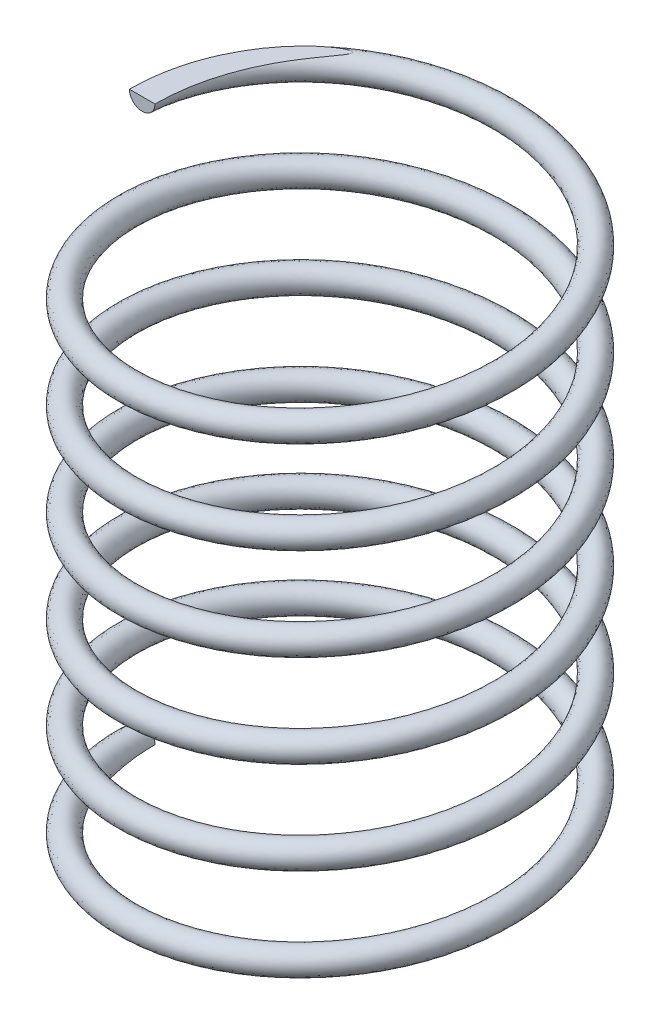
SolidWorks part; units mm, degrees
ref_plane "Front Plane" through (0, 0, 0) normal (0, 0, 1) x (1, 0, 0)
ref_plane "Top Plane" through (0, 0, 0) normal (0, 1, 0) x (1, 0, 0)
ref_plane "Right Plane" through (0, 0, 0) normal (1, 0, 0) x (0, 0, -1)
sketch "Sketch1" plane through (0, 0, 0) normal (0, 1, 0) x (1, 0, 0)
  circle A1 centre (0, 0) radius 4.4
  dimension "D1" = 8.8
curve "Helix/Spiral1" pitch 2.1667 height 13 turns 6
sketch "Sketch5" plane through (0, 0, 0) normal (0, 0, 1) x (1, 0, 0)
  circle A0 centre (-4.4, 0) radius 0.3
  spline S0 degree 3 poles (-4.4, 0) (-4.4, -0.0449) (-4.1709, -0.1356) (-3.1923, -0.2708) (-1.7276, -0.4063) (0, -0.5417) (1.7276, -0.6771) (3.1923, -0.8125) (4.1709, -0.9479) (4.5145, -1.0833) (4.1709, -1.2188) (3.1923, -1.3542) (1.7276, -1.4896) (0, -1.625) (-1.7276, -1.7604) (-3.1923, -1.8958) (-4.1709, -2.0313) (-4.5145, -2.1667) (-4.1709, -2.3021) (-3.1923, -2.4375) (-1.7276, -2.5729) (0, -2.7083) (1.7276, -2.8438) (3.1923, -2.9792) (4.1709, -3.1146) (4.5145, -3.25) (4.1709, -3.3854) (3.1923, -3.5208) (1.7276, -3.6562) (0, -3.7917) (-1.7276, -3.9271) (-3.1923, -4.0625) (-4.1709, -4.1979) (-4.5145, -4.3333) (-4.1709, -4.4687) (-3.1923, -4.6042) (-1.7276, -4.7396) (0, -4.875) (1.7276, -5.0104) (3.1923, -5.1458) (4.1709, -5.2812) (4.5145, -5.4167) (4.1709, -5.5521) (3.1923, -5.6875) (1.7276, -5.8229) (0, -5.9583) (-1.7276, -6.0937) (-3.1923, -6.2292) (-4.1709, -6.3646) (-4.5145, -6.5) (-4.1709, -6.6354) (-3.1923, -6.7708) (-1.7276, -6.9062) (0, -7.0417) (1.7276, -7.1771) (3.1923, -7.3125) (4.1709, -7.4479) (4.5145, -7.5833) (4.1709, -7.7187) (3.1923, -7.8542) (1.7276, -7.9896) (0, -8.125) (-1.7276, -8.2604) (-3.1923, -8.3958) (-4.1709, -8.5312) (-4.5145, -8.6667) (-4.1709, -8.8021) (-3.1923, -8.9375) (-1.7276, -9.0729) (0, -9.2083) (1.7276, -9.3438) (3.1923, -9.4792) (4.1709, -9.6146) (4.5145, -9.75) (4.1709, -9.8854) (3.1923, -10.0208) (1.7276, -10.1563) (0, -10.2917) (-1.7276, -10.4271) (-3.1923, -10.5625) (-4.1709, -10.6979) (-4.5145, -10.8333) (-4.1709, -10.9687) (-3.1923, -11.1042) (-1.7276, -11.2396) (0, -11.375) (1.7276, -11.5104) (3.1923, -11.6458) (4.1709, -11.7812) (4.5145, -11.9167) (4.1709, -12.0521) (3.1923, -12.1875) (1.7276, -12.3229) (0, -12.4583) (-1.7276, -12.5937) (-3.1923, -12.7292) (-4.1709, -12.8644) (-4.4, -12.9551) (-4.4, -13) knots 0 0 0 0 0.010417 0.020833 0.03125 0.041667 0.052083 0.0625 0.072917 0.083333 0.09375 0.104167 0.114583 0.125 0.135417 0.145833 0.15625 0.166667 0.177083 0.1875 0.197917 0.208333 0.21875 0.229167 0.239583 0.25 0.260417 0.270833 0.28125 0.291667 0.302083 0.3125 0.322917 0.333333 0.34375 0.354167 0.364583 0.375 0.385417 0.395833 0.40625 0.416667 0.427083 0.4375 0.447917 0.458333 0.46875 0.479167 0.489583 0.5 0.510417 0.520833 0.53125 0.541667 0.552083 0.5625 0.572917 0.583333 0.59375 0.604167 0.614583 0.625 0.635417 0.645833 0.65625 0.666667 0.677083 0.6875 0.697917 0.708333 0.71875 0.729167 0.739583 0.75 0.760417 0.770833 0.78125 0.791667 0.802083 0.8125 0.822917 0.833333 0.84375 0.854167 0.864583 0.875 0.885417 0.895833 0.90625 0.916667 0.927083 0.9375 0.947917 0.958333 0.96875 0.979167 0.989583 1 1 1 1 construction
  dimension "D1" = 0.6
sweep "Sweep2" add profiles "Sketch5" path "Helix/Spiral1"
other "SurfaceCut4" [suppressed]
ref_plane "Plane3" through (0, -13, 0) normal (0, 1, 0) x (1, 0, 0)
other "SurfaceCut5"
other "SurfaceCut6"
